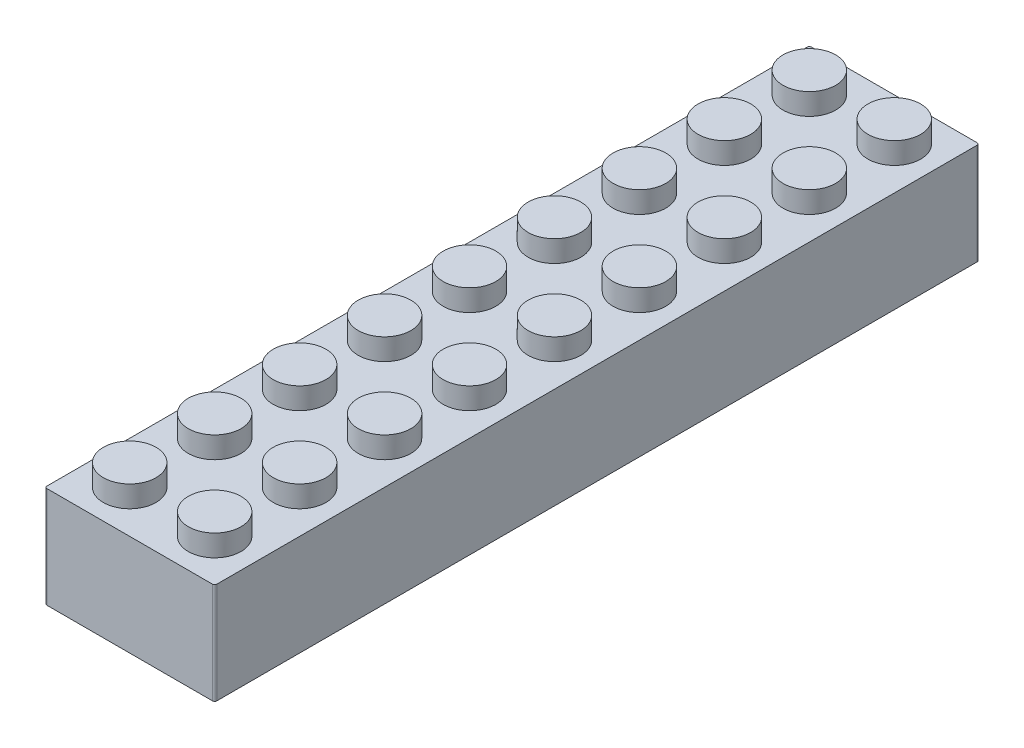
SolidWorks part; units mm, degrees
ref_plane "Front Plane" through (0, 0, 0) normal (0, 0, 1) x (1, 0, 0)
ref_plane "Top Plane" through (0, 0, 0) normal (0, 1, 0) x (1, 0, 0)
ref_plane "Right Plane" through (0, 0, 0) normal (1, 0, 0) x (0, 0, -1)
sketch "stencil" plane through (0, 0, 0) normal (0, 1, 0) x (1, 0, 0)
  line L2 (7.9, 71.1) -> (7.9, 0) construction
  line L29 (14.35, 1.45) -> (1.45, 1.45)
  line L30 (15.75, 71.05) -> (0.05, 71.05)
  line L32 (15.75, 71.05) -> (15.75, 0.05)
  line L34 (15.75, 0.05) -> (0.05, 0.05)
  line L36 (0.05, 71.05) -> (0.05, 0.05)
  line L37 (7.9, 0.05) -> (7.9, 71.05) construction
  line L38 (15.75, 35.55) -> (0.05, 35.55) construction
  line L39 (1.45, 69.65) -> (1.45, 1.45)
  line L40 (14.35, 69.65) -> (1.45, 69.65)
  line L41 (14.35, 69.65) -> (14.35, 1.45)
  circle A40 centre (3.95, 3.95) radius 2.45
  circle A41 centre (7.9, 7.9) radius 3.2
  circle A42 centre (3.95, 11.85) radius 2.45
  circle A43 centre (3.95, 19.75) radius 2.45
  circle A44 centre (3.95, 27.65) radius 2.45
  circle A45 centre (7.9, 15.8) radius 3.2
  circle A46 centre (7.9, 23.7) radius 3.2
  circle A47 centre (7.9, 31.6) radius 3.2
  circle A48 centre (3.95, 35.55) radius 2.45
  circle A49 centre (3.95, 43.45) radius 2.45
  circle A50 centre (3.95, 51.35) radius 2.45
  circle A51 centre (7.9, 39.5) radius 3.2
  circle A52 centre (7.9, 47.4) radius 3.2
  circle A53 centre (3.95, 59.25) radius 2.45
  circle A54 centre (3.95, 67.15) radius 2.45
  circle A55 centre (7.9, 55.3) radius 3.2
  circle A56 centre (7.9, 63.2) radius 3.2
  circle A57 centre (7.9, 7.9) radius 2.4
  circle A58 centre (7.9, 15.8) radius 2.4
  circle A59 centre (7.9, 23.7) radius 2.4
  circle A60 centre (7.9, 31.6) radius 2.4
  circle A61 centre (7.9, 39.5) radius 2.4
  circle A62 centre (7.9, 47.4) radius 2.4
  circle A63 centre (7.9, 55.3) radius 2.4
  circle A64 centre (7.9, 63.2) radius 2.4
  circle A65 centre (11.85, 11.85) radius 2.45
  circle A66 centre (11.85, 19.75) radius 2.45
  circle A67 centre (11.85, 27.65) radius 2.45
  circle A68 centre (11.85, 35.55) radius 2.45
  circle A69 centre (11.85, 43.45) radius 2.45
  circle A70 centre (11.85, 51.35) radius 2.45
  circle A71 centre (11.85, 59.25) radius 2.45
  circle A72 centre (11.85, 67.15) radius 2.45
  circle A73 centre (11.85, 3.95) radius 2.45
  point P1 (0, 0)
  point P6 (3.95, -15.8)
  point P9 (7.9, -15.8)
  point P10 (7.9, -11.85)
  point P13 (3.95, -7.9)
  point P15 (7.9, -7.9)
  point P17 (7.9, -3.95)
  point P18 (3.95, 0)
  point P21 (7.9, 0)
  point P25 (7.9, 3.95)
  point P27 (3.95, 7.9)
  point P28 (7.9, 7.9)
  point P29 (0, -11.85)
  point P30 (0, -7.9)
  point P31 (0, 3.95)
  point P34 (0, -3.95)
  point P35 (3.95, 0)
  point P36 (0, 15.8)
  point P37 (0, 23.7)
  point P38 (7.9, 23.7)
  point P39 (15.8, 23.7)
  point P40 (15.8, 15.8)
  point P41 (15.8, 7.9)
  point P43 (7.9, 0)
  point P48 (11.85, 0)
  point P49 (15.8, 0)
  point P50 (3.95, 3.95)
  point P51 (7.9, 3.95)
  point P52 (11.85, 3.95)
  point P53 (15.8, 3.95)
  point P54 (3.95, 7.9)
  point P55 (7.9, 7.9)
  point P56 (11.85, 7.9)
  point P57 (15.8, 7.9)
  point P58 (3.95, 11.85)
  point P59 (7.9, 11.85)
  point P60 (11.85, 11.85)
  point P61 (15.8, 11.85)
  point P63 (3.95, 15.8)
  point P64 (7.9, 15.8)
  point P65 (11.85, 15.8)
  point P66 (15.8, 15.8)
  point P67 (3.95, 19.75)
  point P68 (7.9, 19.75)
  point P69 (11.85, 19.75)
  point P70 (15.8, 19.75)
  point P71 (3.95, 23.7)
  point P72 (7.9, 23.7)
  point P73 (11.85, 23.7)
  point P75 (15.8, 23.7)
  point P77 (3.95, 27.65)
  point P79 (7.9, 27.65)
  point P81 (11.85, 27.65)
  point P83 (15.8, 27.65)
  point P85 (3.95, 31.6)
  point P87 (7.9, 31.6)
  point P88 (11.85, 31.6)
  point P89 (15.8, 31.6)
  point P90 (0, 3.95)
  point P91 (0, 7.9)
  point P92 (0, 11.85)
  point P93 (0, 15.8)
  point P94 (0, 19.75)
  point P95 (0, 23.7)
  point P96 (0, 27.65)
  point P97 (0, 31.6)
  point P113 (0, 35.55)
  point P114 (3.95, 35.55)
  point P115 (7.9, 35.55)
  point P116 (11.85, 35.55)
  point P117 (15.8, 35.55)
  point P118 (0, 39.5)
  point P119 (3.95, 39.5)
  point P120 (7.9, 39.5)
  point P121 (11.85, 39.5)
  point P122 (15.8, 39.5)
  point P124 (0, 43.45)
  point P125 (3.95, 43.45)
  point P126 (7.9, 43.45)
  point P127 (11.85, 43.45)
  point P128 (15.8, 43.45)
  point P129 (0, 47.4)
  point P130 (3.95, 47.4)
  point P131 (7.9, 47.4)
  point P132 (11.85, 47.4)
  point P133 (15.8, 47.4)
  point P135 (0, 51.35)
  point P136 (3.95, 51.35)
  point P137 (7.9, 51.35)
  point P138 (11.85, 51.35)
  point P139 (15.8, 51.35)
  point P140 (0, 55.3)
  point P141 (3.95, 55.3)
  point P142 (7.9, 55.3)
  point P143 (11.85, 55.3)
  point P144 (15.8, 55.3)
  point P145 (0, 59.25)
  point P146 (3.95, 59.25)
  point P147 (7.9, 59.25)
  point P148 (11.85, 59.25)
  point P149 (15.8, 59.25)
  point P150 (0, 63.2)
  point P151 (3.95, 63.2)
  point P152 (7.9, 63.2)
  point P153 (11.85, 63.2)
  point P154 (15.8, 63.2)
  point P165 (0, 67.15)
  point P166 (3.95, 67.15)
  point P167 (7.9, 67.15)
  point P168 (11.85, 67.15)
  point P169 (15.8, 67.15)
  point P170 (0, 71.1)
  point P171 (3.95, 71.1)
  point P172 (7.9, 71.1)
  point P173 (11.85, 71.1)
  point P174 (15.8, 71.1)
  point P182 (7.9, 35.55)
  dimension "D8" = 4.9
  dimension "D9" = 6.4
  dimension "D3" = 3.95
  dimension "D4" = 3.95
  dimension "D5" = 15.7
  dimension "D6" = 71
  dimension "D7" = 0.8
  dimension "D10" = 1.4
  dimension "D1" = 5
sketch "Sketch1" plane through (0, 0, 0) normal (0, 1, 0) x (1, 0, 0)
  line L1 (15.8, 71.1) -> (0, 71.1)
  line L2 (15.8, 71.1) -> (15.8, 0)
  line L3 (15.8, 0) -> (0, 0)
  line L4 (0, 71.1) -> (0, 0)
  line L5 (7.9, 0) -> (7.9, 71.1) construction
  line L6 (15.8, 35.55) -> (0, 35.55) construction
  point P0 (7.9, 35.55)
extrude "Boss-Extrude1" add sketch "Sketch1" along normal mid plane 9.4
sketch "Sketch2" plane through (0, 4.7, 0) normal (0, 1, 0) x (1, 0, 0)
  line L0 (0, 71.1) -> (0, 0) construction
  circle A0 centre (3.95, 3.95) radius 2.45
  circle A1 centre (11.85, 3.95) radius 2.45
  circle A2 centre (11.85, 11.85) radius 2.45
  circle A3 centre (3.95, 11.85) radius 2.45
  circle A4 centre (3.95, 19.75) radius 2.45
  circle A5 centre (3.95, 27.65) radius 2.45
  circle A6 centre (11.85, 27.65) radius 2.45
  circle A7 centre (11.85, 35.55) radius 2.45
  circle A8 centre (3.95, 35.55) radius 2.45
  circle A9 centre (3.95, 43.45) radius 2.45
  circle A10 centre (11.85, 43.45) radius 2.45
  circle A11 centre (3.95, 51.35) radius 2.45
  circle A12 centre (11.85, 51.35) radius 2.45
  circle A13 centre (3.95, 59.25) radius 2.45
  circle A14 centre (11.85, 59.25) radius 2.45
  circle A15 centre (3.95, 67.15) radius 2.45
  circle A16 centre (11.85, 67.15) radius 2.45
  circle A17 centre (3.95, 3.95) radius 2.45 construction
  circle A18 centre (11.85, 19.75) radius 2.45
  circle A19 centre (11.85, 19.75) radius 2.45 construction
extrude "Boss-Extrude2" add sketch "Sketch2" along normal blind 2
sketch "Sketch3" plane through (0, -4.7, 0) normal (0, -1, 0) x (1, 0, 0)
  line L1 (14.35, -1.45) -> (1.45, -1.45)
  line L2 (14.35, -1.45) -> (14.35, -69.65)
  line L3 (14.35, -69.65) -> (1.45, -69.65)
  line L4 (1.45, -1.45) -> (1.45, -69.65)
  line L5 (7.9, -69.65) -> (7.9, -1.45) construction
  line L6 (14.35, -35.55) -> (1.45, -35.55) construction
  point P0 (7.9, -35.55)
extrude "Cut-Extrude1" cut sketch "Sketch3" against normal blind 4
sketch "Sketch4" plane through (0, -0.7, 0) normal (0, -1, 0) x (1, 0, 0)
  circle A0 centre (7.9, -63.2) radius 3.2
  circle A1 centre (7.9, -55.3) radius 3.2
  circle A2 centre (7.9, -47.4) radius 3.2
  circle A3 centre (7.9, -39.5) radius 3.2
  circle A4 centre (7.9, -31.6) radius 3.2
  circle A5 centre (7.9, -23.7) radius 3.2
  circle A6 centre (7.9, -15.8) radius 3.2
  circle A7 centre (7.9, -7.9) radius 3.2
  circle A8 centre (7.9, -7.9) radius 2.4
  circle A10 centre (7.9, -15.8) radius 2.4
  circle A11 centre (7.9, -23.7) radius 2.4
  circle A12 centre (7.9, -31.6) radius 2.4
  circle A13 centre (7.9, -39.5) radius 2.4
  circle A14 centre (7.9, -47.4) radius 2.4
  circle A15 centre (7.9, -55.3) radius 2.4
  circle A16 centre (7.9, -63.2) radius 2.4
  circle A17 centre (7.9, -63.2) radius 2.4 construction
  circle A18 centre (7.9, -63.2) radius 3.2 construction
extrude "Boss-Extrude3" add sketch "Sketch4" along normal up to surface (4 mm away) up to face at (7.9, -4.7, -35.55)
fillet "Fillet1" radius 0.2 4 edges at (0, 0, -71.1) (15.8, 0, -71.1) (0, 0, 0) (15.8, 0, 0)
equation "\"t\"= 0.1'tolerance"
equation "\"D5@stencil\"=15.80-\"t\""
equation "\"D10@stencil\"=1.5-\"t\""
equation "\"D6@stencil\"=71.10mm-\"t\""
equation "\"D9@stencil\"=6.50-\"t\""
equation "\"D1@Boss-Extrude1\"=9.5-\"t\""
